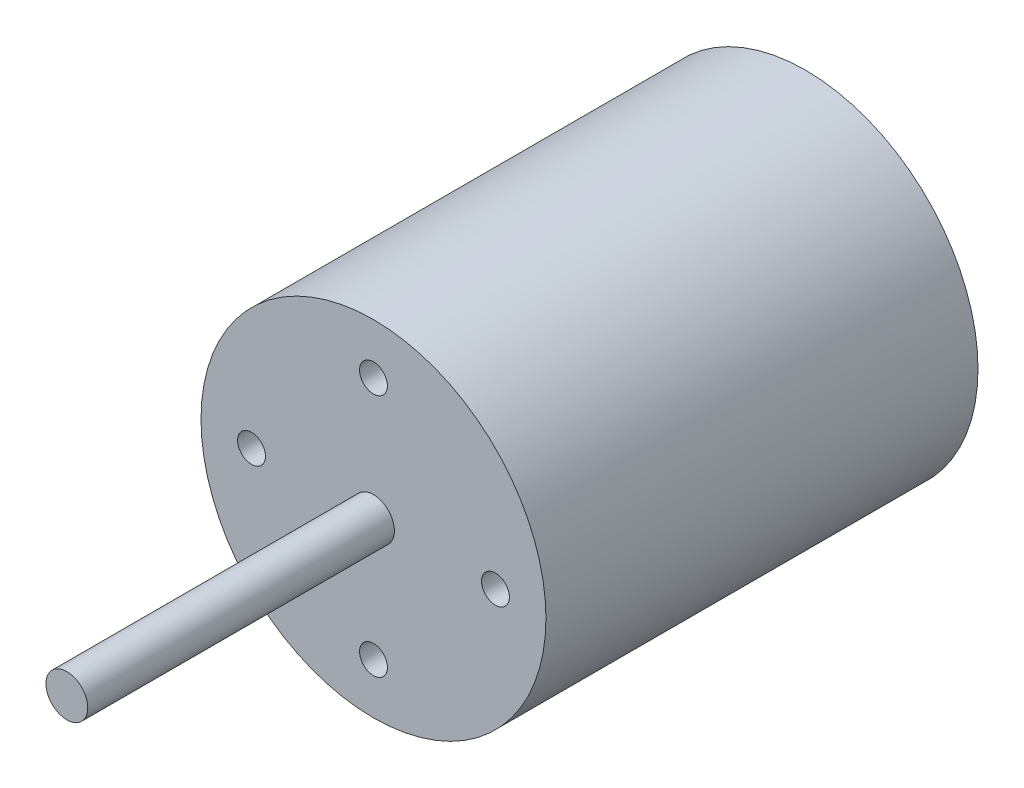
SolidWorks part; units mm, degrees
ref_plane "Front Plane" through (0, 0, 0) normal (0, 0, 1) x (1, 0, 0)
ref_plane "Top Plane" through (0, 0, 0) normal (0, 1, 0) x (1, 0, 0)
ref_plane "Right Plane" through (0, 0, 0) normal (1, 0, 0) x (0, 0, -1)
sketch "Sketch1" plane through (0, 0, 0) normal (0, 0, 1) x (1, 0, 0)
  circle A0 centre (0, 0) radius 24.75
  dimension "D1" = 49.5
extrude "Boss-Extrude1" add sketch "Sketch1" against normal mid plane 62
sketch "Sketch2" plane through (0, 0, 31) normal (0, 0, 1) x (1, 0, 0)
  circle A0 centre (0, 0) radius 3
  dimension "D1" = 6
extrude "Boss-Extrude2" add sketch "Sketch2" along normal blind 44
sketch "Sketch6" plane through (0, 0, 31) normal (0, 0, 1) x (1, 0, 0)
  circle A0 centre (0, 0) radius 17.5 construction
  circle A1 centre (0, 17.5) radius 2
  dimension "D1" = 4
  dimension "D5" = 35
extrude "Cut-Extrude3" cut sketch "Sketch6" against normal blind 5
pattern_circular "CirPattern1" count 4 over 360 about axis through (0, 0, 0) along (0, 0, 1) of "Cut-Extrude3"
sketch "Sketch5" plane through (0, 0, -31) normal (0, 0, -1) x (-1, 0, 0)
  circle A0 centre (0, 0) radius 17.5 construction
  circle A1 centre (-17.5, 0) radius 2
  dimension "D1" = 35
  dimension "D2" = 4
extrude "Cut-Extrude2" cut sketch "Sketch5" against normal blind 10
pattern_circular "CirPattern2" count 2 over 360 about axis through (0, 0, 0) along (0, 0, 1) of "Cut-Extrude2"
sketch "Sketch7" plane through (0, 0, -31) normal (0, 0, -1) x (-1, 0, 0)
  circle A0 centre (0, 0) radius 9
  dimension "D1" = 18
extrude "Boss-Extrude3" add sketch "Sketch7" along normal blind 7
